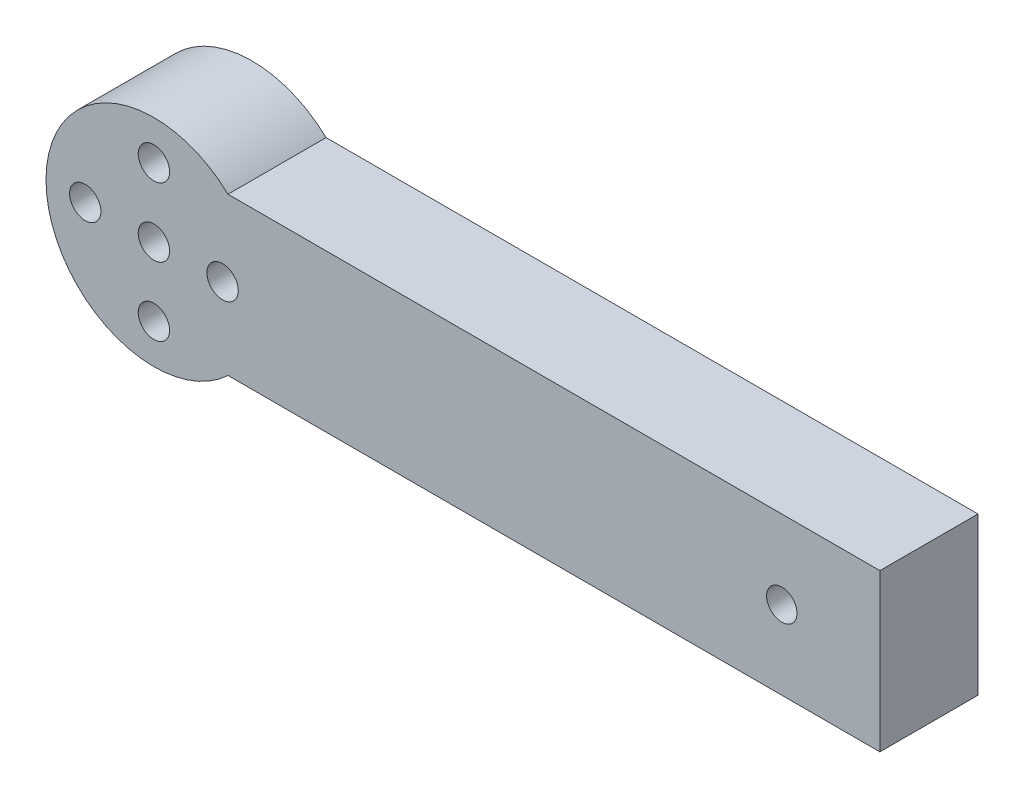
SolidWorks part; units mm, degrees
other "Markup1"
sketch "Sketch2" plane through (82, 11, 10) normal (0.0061, 0.0329, 0.9994) x (0.0023, 0.9995, -0.0329)
material "Carbon Sandwich"
ref_plane "Front Plane" through (0, 0, 0) normal (0, 0, 1) x (1, 0, 0)
ref_plane "Top Plane" through (0, 0, 0) normal (0, 1, 0) x (1, 0, 0)
ref_plane "Right Plane" through (0, 0, 0) normal (1, 0, 0) x (0, 0, -1)
sketch "Sketch1" plane through (0, 0, 0) normal (0, 0, 1) x (1, 0, 0)
  line L0 (0, 0) -> (98, 0) construction
  line L5 (53, -8) -> (53, 8) construction
  line L6 (82, 8) -> (82, -8)
  line L12 (82, 8) -> (15.5498, 8)
  line L13 (82, -8) -> (15.5498, -8)
  circle A0 centre (8, 0) radius 7 construction
  circle A10 centre (8, 7) radius 1.6
  circle A11 centre (1, 0) radius 1.6
  circle A12 centre (8, -7) radius 1.6
  circle A13 centre (15, 0) radius 1.6
  circle A14 centre (8, 0) radius 11 construction
  arc A16 (15.5498, 8) -> (15.5498, -8) centre (8, 0) ccw
  circle A18 centre (8, 0) radius 1.6
  circle A19 centre (72, 0) radius 1.55
  dimension "D3" = 14
  dimension "D4" = 90
  dimension "D6" = 16
  dimension "D9" = 3.2
  dimension "D2" = 22
  dimension "D10" = 10
  dimension "D12" = 3.2
  dimension "D8" = 3.1
  dimension "D5" = 8
  dimension "D7" = 16
  dimension "D11" = 45
extrude "Boss-Extrude1" add sketch "Sketch1" along normal blind 10
